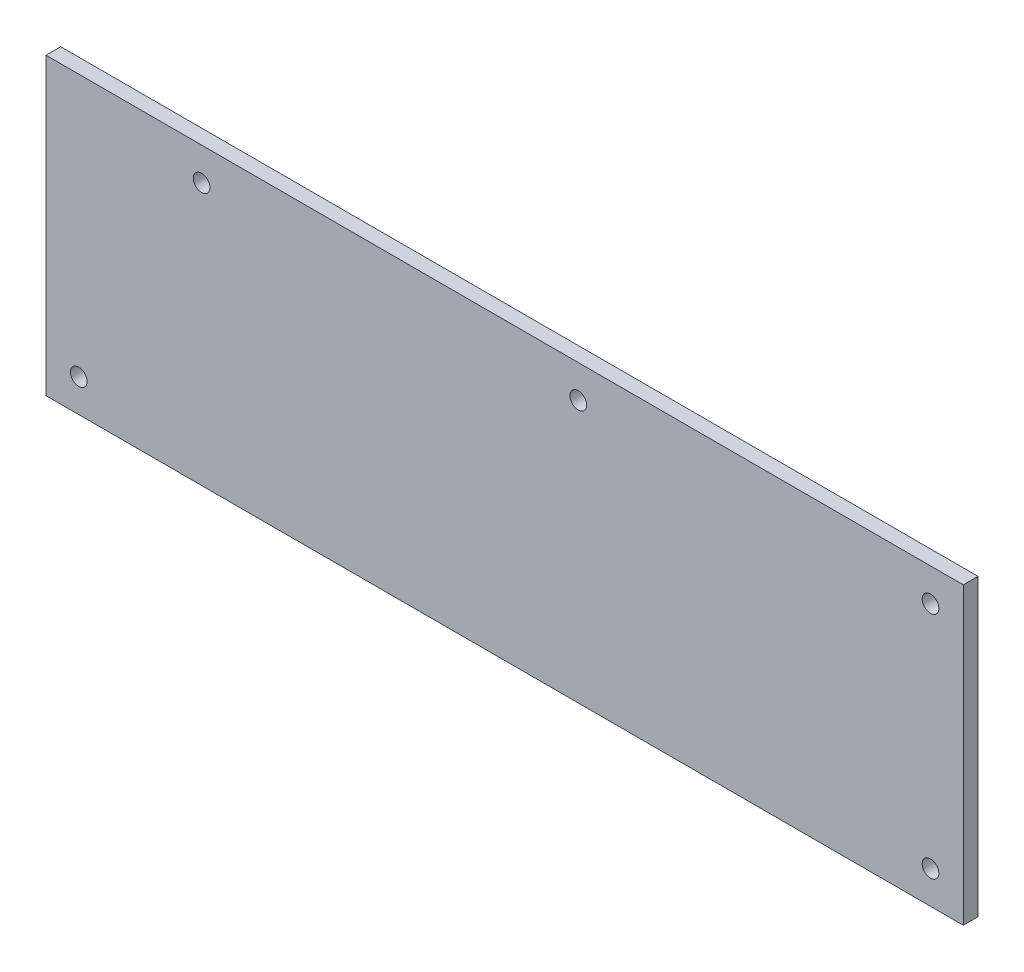
SolidWorks part; units mm, degrees
material "Acrylic (Medium-high impact)"
ref_plane "Front Plane" through (0, 0, 0) normal (0, 0, 1) x (1, 0, 0)
ref_plane "Top Plane" through (0, 0, 0) normal (0, 1, 0) x (1, 0, 0)
ref_plane "Right Plane" through (0, 0, 0) normal (1, 0, 0) x (0, 0, -1)
sketch "Sketch1" plane through (0, 0, 0) normal (0, 0, 1) x (1, 0, 0)
  line L0 (-222.5, 45) -> (-222.5, -45) construction
  line L1 (-232.5, -45) -> (232.5, -45)
  line L2 (-232.5, -45) -> (-232.5, 45)
  line L3 (-232.5, 45) -> (232.5, 45)
  line L4 (232.5, -45) -> (232.5, 45)
  line L5 (-232.5, -45) -> (232.5, 45) construction
  line L6 (-232.5, 45) -> (232.5, -45) construction
  line L7 (0, 45) -> (0, -45) construction
  line L8 (-232.5, 35) -> (2.55, 35) construction
  circle A0 centre (-222.5, 35) radius 2.55
  circle A1 centre (-222.5, -35) radius 2.55
  circle A2 centre (0, 35) radius 2.55
  circle A3 centre (-114.975, 35) radius 2.55
  circle A4 centre (222.5, -35) radius 2.55
  circle A5 centre (222.5, 35) radius 2.55
  circle A6 centre (114.975, 35) radius 2.55
  point P0 (0, 0)
  point P17 (-114.975, 35)
  dimension "D4" = 5.1
  dimension "D5" = 10
  dimension "D6" = 10
  dimension "D7" = 10
  dimension "D1" = 465
  dimension "D2" = 90
  dimension "D3" = 10
extrude "Boss-Extrude1" add sketch "Sketch1" along normal mid plane 4.4958
sketch "Sketch2" plane through (0, 0, -2.2479) normal (0, 0, -1) x (-1, 0, 0)
  line L0 (232.5, -45) -> (-232.5, -45) construction
  line L1 (232.5, 45) -> (47.5, 45)
  line L2 (232.5, 45) -> (232.5, -45)
  line L3 (232.5, -45) -> (47.5, -45)
  line L4 (47.5, 45) -> (47.5, -45)
  line L5 (48.5, -43.0015) -> (48.5, 40) construction
  dimension "D1" = 1
extrude "Cut-Extrude1" cut sketch "Sketch2" against normal up to next
sketch "Sketch3" plane through (0, 0, -2.2479) normal (0, 0, -1) x (-1, 0, 0)
  line L0 (47.5, 45) -> (47.5, -45) construction
  line L1 (47.5, -45) -> (-232.5, -45) construction
  circle A0 centre (37.5, -35) radius 2.55
  dimension "D1" = 5.1
  dimension "D2" = 10
  dimension "D3" = 10
extrude "Cut-Extrude2" cut sketch "Sketch3" against normal up to next
sketch "Sketch4" plane through (0, 0, -2.2479) normal (0, 0, -1) x (-1, 0, 0)
  line L0 (-232.5, -15) -> (47.5, -15) construction
  line L3 (-232.5, -45) -> (-232.5, 45) construction
  line L4 (47.5, 45) -> (47.5, -45) construction
  line L5 (-232.5, -30) -> (47.5, -30) construction
  text T0 "EUSTATHIOS" font "Impact" height 30
  text T1 "SPIDER V2        " font "Adobe Gothic Std B" height 10
  point P6 (-232.5, 0)
  dimension "D1" = 15
  dimension "D2" = 15
extrude "Cut-Extrude3" cut sketch "Sketch4" against normal blind 1
